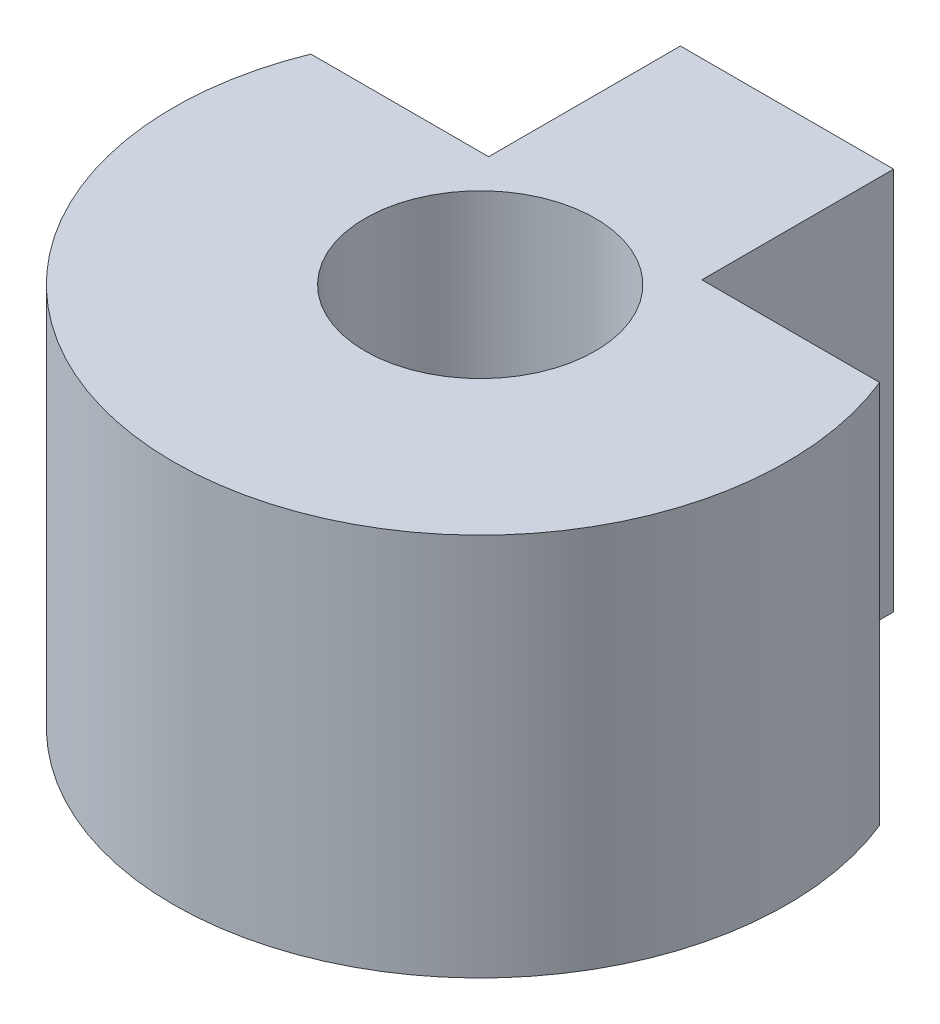
SolidWorks part; units mm, degrees
material "Polyurethane Foam Rigid"
ref_plane "Front Plane" through (0, 0, 0) normal (0, 0, 1) x (1, 0, 0)
ref_plane "Top Plane" through (0, 0, 0) normal (0, 1, 0) x (1, 0, 0)
ref_plane "Right Plane" through (0, 0, 0) normal (1, 0, 0) x (0, 0, -1)
sketch "Sketch1" plane through (0, 0, 0) normal (0, 1, 0) x (1, 0, 0)
  line L0 (0, 5.08) -> (0, 0) construction
  line L2 (-1.7653, 1.905) -> (-1.7653, 5.08)
  line L3 (-1.7653, 5.08) -> (1.7653, 5.08)
  line L4 (1.7653, 1.905) -> (1.7653, 5.08)
  line L5 (-1.7653, 1.905) -> (-4.7093, 1.905)
  line L6 (1.7653, 1.905) -> (4.7093, 1.905)
  circle A0 centre (0, 0) radius 1.905
  arc A1 (-4.7093, 1.905) -> (4.7093, 1.905) centre (0, 0) ccw
  dimension "D1" = 3.81
  dimension "D2" = 3.175
  dimension "D4" = 3.175
  dimension "D3" = 3.5306
extrude "Boss-Extrude1" add sketch "Sketch1" along normal blind 6.35
